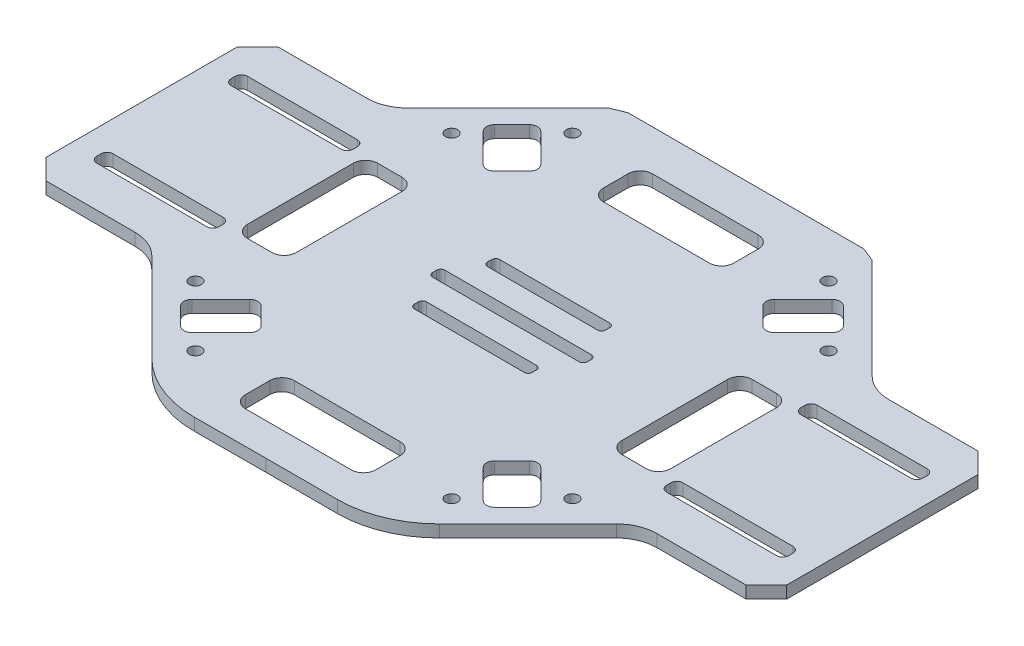
SolidWorks part; units mm, degrees
ref_plane "Спереди" through (0, 0, 0) normal (0, 0, 1) x (1, 0, 0)
ref_plane "Сверху" through (0, 0, 0) normal (0, 1, 0) x (1, 0, 0)
ref_plane "Справа" through (0, 0, 0) normal (1, 0, 0) x (0, 0, -1)
sketch "Эскиз1" plane through (0, 0, 0) normal (0, 1, 0) x (1, 0, 0)
  line L0 (-47.2118, 0) -> (134.7882, 0) construction
  line L1 (43.7882, 0) -> (43.7882, 85.4485) construction
  line L2 (134.7882, -23.5) -> (134.7882, 23.5)
  line L3 (-47.2118, -23.5) -> (-47.2118, 23.5)
  line L4 (134.7882, 0) -> (134.7882, 1.9061) construction
  line L5 (43.7882, 0) -> (43.7882, -60.5) construction
  line L6 (-47.2118, 23.5) -> (-42.2118, 28.5)
  line L7 (61.7882, 1.5) -> (25.7882, 1.5)
  line L8 (61.7882, -1.5) -> (25.7882, -1.5)
  line L9 (129.7882, 28.5) -> (107.9304, 28.5)
  line L10 (129.7882, -28.5) -> (107.9304, -28.5)
  line L11 (-42.2118, -28.5) -> (-20.3539, -28.5)
  line L12 (-42.2118, 28.5) -> (-20.3539, 28.5)
  line L13 (43.7882, 57.5) -> (71.7882, 57.5)
  line L14 (43.7882, 57.5) -> (15.7882, 57.5)
  line L15 (3.0731, -40.7138) -> (43.7882, 0) construction
  line L16 (15.7882, 57.5) -> (14.7882, 57.5)
  line L17 (43.7882, -7.5) -> (57.2882, -7.5)
  line L18 (24.7882, 0.5) -> (24.7882, -0.5)
  line L19 (43.7882, -7.5) -> (30.2882, -7.5)
  line L20 (58.2882, -8.5) -> (58.2882, -9.5)
  line L21 (62.7882, 0.5) -> (62.7882, -0.5)
  line L22 (57.2882, -10.5) -> (30.2882, -10.5)
  line L23 (29.2882, -9.5) -> (29.2882, -8.5)
  line L24 (-42.2118, -28.5) -> (-47.2118, -23.5)
  line L25 (29.2882, 9.5) -> (29.2882, 8.5)
  line L26 (57.2882, 10.5) -> (30.2882, 10.5)
  line L27 (58.2882, 8.5) -> (58.2882, 9.5)
  line L28 (43.7882, 7.5) -> (30.2882, 7.5)
  line L29 (43.7882, 7.5) -> (57.2882, 7.5)
  line L30 (-16.2118, -28.5) -> (15.8899, -60.6016) construction
  line L31 (100.8593, -31.4289) -> (79.1106, -53.1777)
  line L32 (43.7882, -60.5) -> (61.4329, -60.5)
  line L33 (43.7882, 0) -> (84.5034, 40.7138) construction
  line L34 (88.0376, 44.2507) -> (84.5034, 40.7138) construction
  line L35 (3.0731, -40.7138) -> (-0.4624, -44.2493) construction
  line L36 (43.7882, -60.5) -> (26.2985, -60.5637)
  line L37 (43.7882, 0) -> (84.5034, -40.7138) construction
  line L38 (128.7882, -17) -> (128.7882, -16)
  line L39 (127.2882, -14.5) -> (100.2882, -14.5)
  line L40 (128.7882, 17) -> (128.7882, 16)
  line L41 (127.2882, 14.5) -> (100.2882, 14.5)
  line L42 (98.7882, 16) -> (98.7882, 17)
  line L43 (100.2882, 18.5) -> (127.2882, 18.5)
  line L44 (98.7882, -16) -> (98.7882, -17)
  line L45 (100.2882, -18.5) -> (127.2882, -18.5)
  line L46 (-41.2118, -17) -> (-41.2118, -16)
  line L47 (-12.7118, -18.5) -> (-39.7118, -18.5)
  line L48 (-11.2118, -16) -> (-11.2118, -17)
  line L49 (-39.7118, -14.5) -> (-12.7118, -14.5)
  line L50 (-11.2118, 16) -> (-11.2118, 17)
  line L51 (-41.2118, 17) -> (-41.2118, 16)
  line L52 (-39.7118, 14.5) -> (-12.7118, 14.5)
  line L53 (-12.7118, 18.5) -> (-39.7118, 18.5)
  line L54 (83.7882, 0) -> (83.7882, 13)
  line L55 (83.7882, 0) -> (83.7882, -13)
  line L56 (134.7882, 0) -> (95.7882, 0) construction
  line L57 (95.7882, 0) -> (95.7882, 13)
  line L58 (92.7882, 16) -> (86.7882, 16)
  line L59 (95.7882, 0) -> (95.7882, -13)
  line L60 (92.7882, -16) -> (86.7882, -16)
  line L61 (-8.2118, 0) -> (-8.2118, 13)
  line L62 (-5.2118, 16) -> (0.7882, 16)
  line L63 (3.7882, 0) -> (3.7882, 13)
  line L64 (3.7882, 0) -> (3.7882, -13)
  line L65 (-5.2118, -16) -> (0.7882, -16)
  line L66 (-8.2118, 0) -> (-8.2118, -13)
  line L67 (86.6247, 35.7641) -> (79.5536, 28.693)
  line L68 (43.7882, -52.5) -> (56.7882, -52.5)
  line L69 (59.7882, -49.5) -> (59.7882, -43.5)
  line L70 (56.7882, -40.5) -> (43.7882, -40.5)
  line L71 (43.7882, -40.5) -> (30.7882, -40.5)
  line L72 (27.7882, -43.5) -> (27.7882, -49.5)
  line L73 (30.7882, -52.5) -> (43.7882, -52.5)
  line L74 (3.0731, 40.7138) -> (5.1944, 42.8351)
  line L75 (43.7882, 47.5) -> (56.7882, 47.5)
  line L76 (43.7882, 47.5) -> (30.7882, 47.5)
  line L77 (27.7882, 44.5) -> (27.7882, 38.5)
  line L78 (30.7882, 35.5) -> (56.7882, 35.5)
  line L79 (59.7882, 38.5) -> (59.7882, 44.5)
  line L80 (3.0731, 40.7138) -> (0.9518, 38.5925)
  line L81 (8.0229, 42.8351) -> (15.0939, 35.7641)
  line L82 (0.9518, 35.7641) -> (8.0229, 28.693)
  line L83 (15.0939, 32.9356) -> (10.8513, 28.693)
  line L84 (72.4825, 32.9356) -> (76.7252, 28.693)
  line L85 (79.5536, 42.8351) -> (72.4825, 35.7641)
  line L86 (84.5034, 40.7138) -> (82.382, 42.8351)
  line L87 (84.5034, 40.7138) -> (86.6247, 38.5925)
  line L88 (3.0731, -40.7138) -> (5.1944, -42.8351)
  line L89 (3.0731, -40.7138) -> (0.9518, -38.5925)
  line L90 (0.9518, -35.7641) -> (8.0229, -28.693)
  line L91 (15.0939, -32.9356) -> (10.8513, -28.693)
  line L92 (8.0229, -42.8351) -> (15.0939, -35.7641)
  line L93 (72.4825, -32.9356) -> (76.7252, -28.693)
  line L94 (86.6247, -35.7641) -> (79.5536, -28.693)
  line L95 (84.5034, -40.7138) -> (86.6247, -38.5925)
  line L96 (84.5034, -40.7138) -> (82.382, -42.8351)
  line L97 (79.5536, -42.8351) -> (72.4825, -35.7641)
  line L98 (8.5298, -53.2416) -> (-13.2828, -31.4289)
  line L99 (84.5034, -40.7138) -> (88.0389, -44.2493) construction
  line L100 (100.8593, 31.4289) -> (76.2024, 56.0858)
  line L101 (71.7882, 57.5) -> (72.7882, 57.5)
  line L102 (-13.2828, 31.4289) -> (11.374, 56.0858)
  line L103 (43.7882, 0) -> (12.9726, 30.8143) construction
  line L104 (12.9726, 30.8143) -> (-0.4624, 44.2493) construction
  line L105 (134.7882, 23.5) -> (129.7882, 28.5)
  line L106 (134.7882, -23.5) -> (129.7882, -28.5)
  line L107 (14.7882, 57.5) -> (11.374, 56.0858)
  line L108 (76.2024, 56.0858) -> (72.7882, 57.5)
  arc A0 (24.7882, -0.5) -> (25.7882, -1.5) centre (25.7882, -0.5) ccw
  arc A1 (25.7882, 1.5) -> (24.7882, 0.5) centre (25.7882, 0.5) ccw
  arc A2 (61.7882, 1.5) -> (62.7882, 0.5) centre (61.7882, 0.5) cw
  arc A3 (62.7882, -0.5) -> (61.7882, -1.5) centre (61.7882, -0.5) cw
  arc A4 (58.2882, -9.5) -> (57.2882, -10.5) centre (57.2882, -9.5) cw
  arc A5 (57.2882, -7.5) -> (58.2882, -8.5) centre (57.2882, -8.5) cw
  arc A6 (30.2882, -7.5) -> (29.2882, -8.5) centre (30.2882, -8.5) ccw
  arc A7 (30.2882, -10.5) -> (29.2882, -9.5) centre (30.2882, -9.5) cw
  arc A8 (30.2882, 7.5) -> (29.2882, 8.5) centre (30.2882, 8.5) cw
  arc A9 (29.2882, 9.5) -> (30.2882, 10.5) centre (30.2882, 9.5) cw
  arc A10 (57.2882, 10.5) -> (58.2882, 9.5) centre (57.2882, 9.5) cw
  arc A11 (58.2882, 8.5) -> (57.2882, 7.5) centre (57.2882, 8.5) cw
  arc A12 (-12.7118, -18.5) -> (-11.2118, -17) centre (-12.7118, -17) ccw
  arc A13 (-11.2118, -16) -> (-12.7118, -14.5) centre (-12.7118, -16) ccw
  arc A14 (-41.2118, -17) -> (-39.7118, -18.5) centre (-39.7118, -17) ccw
  arc A15 (-41.2118, -16) -> (-39.7118, -14.5) centre (-39.7118, -16) cw
  arc A16 (-41.2118, 17) -> (-39.7118, 18.5) centre (-39.7118, 17) cw
  arc A17 (-41.2118, 16) -> (-39.7118, 14.5) centre (-39.7118, 16) ccw
  arc A18 (-11.2118, 16) -> (-12.7118, 14.5) centre (-12.7118, 16) cw
  arc A19 (-11.2118, 17) -> (-12.7118, 18.5) centre (-12.7118, 17) ccw
  arc A20 (128.7882, -17) -> (127.2882, -18.5) centre (127.2882, -17) cw
  arc A21 (128.7882, -16) -> (127.2882, -14.5) centre (127.2882, -16) ccw
  arc A22 (98.7882, -17) -> (100.2882, -18.5) centre (100.2882, -17) ccw
  arc A23 (100.2882, -14.5) -> (98.7882, -16) centre (100.2882, -16) ccw
  arc A24 (128.7882, 16) -> (127.2882, 14.5) centre (127.2882, 16) cw
  arc A25 (128.7882, 17) -> (127.2882, 18.5) centre (127.2882, 17) ccw
  arc A26 (100.2882, 14.5) -> (98.7882, 16) centre (100.2882, 16) cw
  arc A27 (98.7882, 17) -> (100.2882, 18.5) centre (100.2882, 17) cw
  arc A28 (0.9518, 38.5925) -> (0.9518, 35.7641) centre (2.366, 37.1783) ccw
  arc A29 (8.0229, 28.693) -> (10.8513, 28.693) centre (9.4371, 30.1072) ccw
  arc A30 (15.0939, 35.7641) -> (15.0939, 32.9356) centre (13.6797, 34.3498) cw
  arc A31 (5.1944, 42.8351) -> (8.0229, 42.8351) centre (6.6086, 41.4209) cw
  arc A32 (15.0939, -32.9356) -> (15.0939, -35.7641) centre (13.6797, -34.3498) cw
  arc A33 (8.0229, -28.693) -> (10.8513, -28.693) centre (9.4371, -30.1072) cw
  arc A34 (0.9518, -38.5925) -> (0.9518, -35.7641) centre (2.366, -37.1783) cw
  arc A35 (5.1944, -42.8351) -> (8.0229, -42.8351) centre (6.6086, -41.4209) ccw
  arc A36 (82.382, -42.8351) -> (79.5536, -42.8351) centre (80.9678, -41.4209) cw
  arc A37 (86.6247, -35.7641) -> (86.6247, -38.5925) centre (85.2105, -37.1783) cw
  arc A38 (72.4825, -32.9356) -> (72.4825, -35.7641) centre (73.8968, -34.3498) ccw
  arc A39 (76.7252, -28.693) -> (79.5536, -28.693) centre (78.1394, -30.1072) cw
  arc A40 (86.6247, 35.7641) -> (86.6247, 38.5925) centre (85.2105, 37.1783) ccw
  arc A41 (79.5536, 28.693) -> (76.7252, 28.693) centre (78.1394, 30.1072) cw
  arc A42 (72.4825, 32.9356) -> (72.4825, 35.7641) centre (73.8968, 34.3498) cw
  arc A43 (79.5536, 42.8351) -> (82.382, 42.8351) centre (80.9678, 41.4209) cw
  arc A44 (83.7882, 13) -> (86.7882, 16) centre (86.7882, 13) cw
  arc A45 (92.7882, 16) -> (95.7882, 13) centre (92.7882, 13) cw
  arc A46 (95.7882, -13) -> (92.7882, -16) centre (92.7882, -13) cw
  arc A47 (86.7882, -16) -> (83.7882, -13) centre (86.7882, -13) cw
  arc A48 (-5.2118, -16) -> (-8.2118, -13) centre (-5.2118, -13) cw
  arc A49 (3.7882, -13) -> (0.7882, -16) centre (0.7882, -13) cw
  arc A50 (0.7882, 16) -> (3.7882, 13) centre (0.7882, 13) cw
  arc A51 (-8.2118, 13) -> (-5.2118, 16) centre (-5.2118, 13) cw
  arc A52 (27.7882, -49.5) -> (30.7882, -52.5) centre (30.7882, -49.5) ccw
  arc A53 (30.7882, -40.5) -> (27.7882, -43.5) centre (30.7882, -43.5) ccw
  arc A54 (59.7882, -43.5) -> (56.7882, -40.5) centre (56.7882, -43.5) ccw
  arc A55 (56.7882, -52.5) -> (59.7882, -49.5) centre (56.7882, -49.5) ccw
  arc A56 (56.7882, 47.5) -> (59.7882, 44.5) centre (56.7882, 44.5) cw
  arc A57 (56.7882, 35.5) -> (59.7882, 38.5) centre (56.7882, 38.5) ccw
  arc A58 (27.7882, 38.5) -> (30.7882, 35.5) centre (30.7882, 38.5) ccw
  arc A59 (30.7882, 47.5) -> (27.7882, 44.5) centre (30.7882, 44.5) ccw
  arc A60 (107.9304, 28.5) -> (100.8593, 31.4289) centre (107.9304, 38.5) cw
  arc A61 (107.9304, -28.5) -> (100.8593, -31.4289) centre (107.9304, -38.5) ccw
  arc A62 (-20.3539, -28.5) -> (-13.2828, -31.4289) centre (-20.3539, -38.5) cw
  arc A63 (-20.3539, 28.5) -> (-13.2828, 31.4289) centre (-20.3539, 38.5) ccw
  arc A64 (79.1106, -53.1777) -> (61.4329, -60.5) centre (61.4329, -35.5) cw
  arc A65 (26.2985, -60.5637) -> (8.5298, -53.2416) centre (26.2075, -35.5639) cw
  point P3 (134.7882, -28.5)
  point P5 (134.7882, 28.5)
  point P7 (-47.2118, -28.5)
  point P8 (-47.2118, 28.5)
  point P36 (12.7882, 57.5)
  point P100 (74.7882, 57.5)
  point P102 (24.7882, -1.5)
  point P109 (62.7882, -1.5)
  point P112 (58.2882, -10.5)
  point P115 (58.2882, -7.5)
  point P118 (29.2882, -7.5)
  point P121 (29.2882, -10.5)
  point P124 (29.2882, 7.5)
  point P127 (29.2882, 10.5)
  point P130 (58.2882, 10.5)
  point P133 (58.2882, 7.5)
  point P136 (-11.2118, -18.5)
  point P139 (-11.2118, -14.5)
  point P142 (-41.2118, -18.5)
  point P145 (-41.2118, -14.5)
  point P148 (-41.2118, 18.5)
  point P151 (-41.2118, 14.5)
  point P154 (-11.2118, 14.5)
  point P157 (-11.2118, 18.5)
  point P160 (128.7882, -18.5)
  point P163 (128.7882, -14.5)
  point P166 (98.7882, -18.5)
  point P169 (98.7882, -14.5)
  point P172 (128.7882, 14.5)
  point P175 (128.7882, 18.5)
  point P178 (98.7882, 14.5)
  point P181 (98.7882, 18.5)
  point P184 (-0.4624, 37.1783)
  point P187 (9.4371, 27.2788)
  point P190 (16.5081, 34.3498)
  point P193 (6.6086, 44.2493)
  point P196 (16.5081, -34.3498)
  point P199 (9.4371, -27.2788)
  point P202 (-0.4624, -37.1783)
  point P205 (6.6086, -44.2493)
  point P208 (80.9678, -44.2493)
  point P211 (88.0389, -37.1783)
  point P214 (71.0683, -34.3498)
  point P217 (78.1394, -27.2788)
  point P220 (88.0389, 37.1783)
  point P223 (78.1394, 27.2788)
  point P226 (71.0683, 34.3498)
  point P229 (80.9678, 44.2493)
  point P232 (83.7882, 16)
  point P235 (95.7882, 16)
  point P238 (95.7882, -16)
  point P241 (83.7882, -16)
  point P244 (-8.2118, -16)
  point P247 (3.7882, -16)
  point P250 (3.7882, 16)
  point P253 (-8.2118, 16)
  point P264 (27.7882, -52.5)
  point P267 (27.7882, -40.5)
  point P274 (59.7882, 47.5)
  point P277 (59.7882, 35.5)
  point P284 (103.7882, 28.5)
  point P287 (103.7882, -28.5)
  point P293 (-16.2118, 28.5)
  dimension "D19" = 1
  dimension "D20" = 1.5
  dimension "D21" = 2
  dimension "D22" = 2
  dimension "D23" = 3
  dimension "D24" = 3
  dimension "D25" = 10
  dimension "D30" = 25
  dimension "D1" = 31
  dimension "D2" = 5
  dimension "D3" = 14
  dimension "D4" = 5
  dimension "D5" = 14
  dimension "D6" = 31
  dimension "D7" = 57
  dimension "D8" = 57
  dimension "D9" = 38
  dimension "D10" = 57.5
  dimension "D11" = 60.5
  dimension "D12" = 39
  dimension "D13" = 12
  dimension "D14" = 5
  dimension "D15" = 12
  dimension "D16" = 8
  dimension "D17" = 12
  dimension "D18" = 10
extrude "Бобышка-Вытянуть1" add sketch "Эскиз1" along normal blind 3
sketch "Эскиз2" plane through (0, 3, 0) normal (0, 1, 0) x (1, 0, 0)
  line L0 (43.7882, 57.5) -> (43.7882, -60.5) construction
  line L1 (72.7882, 57.5) -> (14.7882, 57.5) construction
  line L2 (134.7882, 0) -> (-47.2118, 0) construction
  line L3 (134.7882, -23.5) -> (134.7882, 23.5) construction
  line L4 (-47.2118, 23.5) -> (-47.2118, -23.5) construction
  line L5 (43.7882, 0) -> (-0.4618, 44.25) construction
  line L6 (11.374, 56.0858) -> (-13.2828, 31.4289) construction
  line L7 (43.7882, 0) -> (88.0382, -44.25) construction
  line L8 (79.1106, -53.1777) -> (100.8593, -31.4289) construction
  line L9 (43.7882, 0) -> (-0.4618, -44.25) construction
  line L10 (-13.2828, -31.4289) -> (8.5298, -53.2416) construction
  line L11 (43.7882, 0) -> (88.0382, 44.25) construction
  line L12 (100.8593, 31.4289) -> (76.2024, 56.0858) construction
  line L13 (75.2545, 46.3155) -> (90.1037, 31.4663) construction
  line L14 (4.8974, 38.8909) -> (12.322, 46.3155) construction
  line L15 (4.8974, 38.8909) -> (-2.5273, 31.4663) construction
  line L16 (-42.2118, -28.5) -> (-20.3539, -28.5) construction
  line L17 (-20.3539, 28.5) -> (-42.2118, 28.5) construction
  circle A0 centre (12.322, 46.3155) radius 1.5
  circle A1 centre (-2.5273, 31.4663) radius 1.5
  circle A2 centre (90.1037, 31.4663) radius 1.5
  circle A3 centre (75.2545, 46.3155) radius 1.5
  circle A4 centre (90.1037, -31.4663) radius 1.5
  circle A5 centre (75.2545, -46.3155) radius 1.5
  circle A6 centre (-2.5273, -31.4663) radius 1.5
  circle A7 centre (12.322, -46.3155) radius 1.5
  point P41 (-31.2828, -28.5)
  dimension "D1" = 10.5
  dimension "D2" = 90
  dimension "D3" = 55
  dimension "D4" = 10.5
  dimension "D5" = 90
  dimension "D6" = 110
  dimension "D7" = 62.9325
  dimension "D8" = 92.631
  dimension "D9" = 55
  dimension "D10" = 110
  dimension "D11" = 62.9325
  dimension "D12" = 92.631
  dimension "D13" = 62.9325
  dimension "D14" = 118
  dimension "D15" = 57.5
  dimension "D16" = 60.5
  dimension "D17" = 57
  dimension "D18" = 111.9866
extrude "Вырез-Вытянуть1" cut sketch "Эскиз2" against normal blind 10
